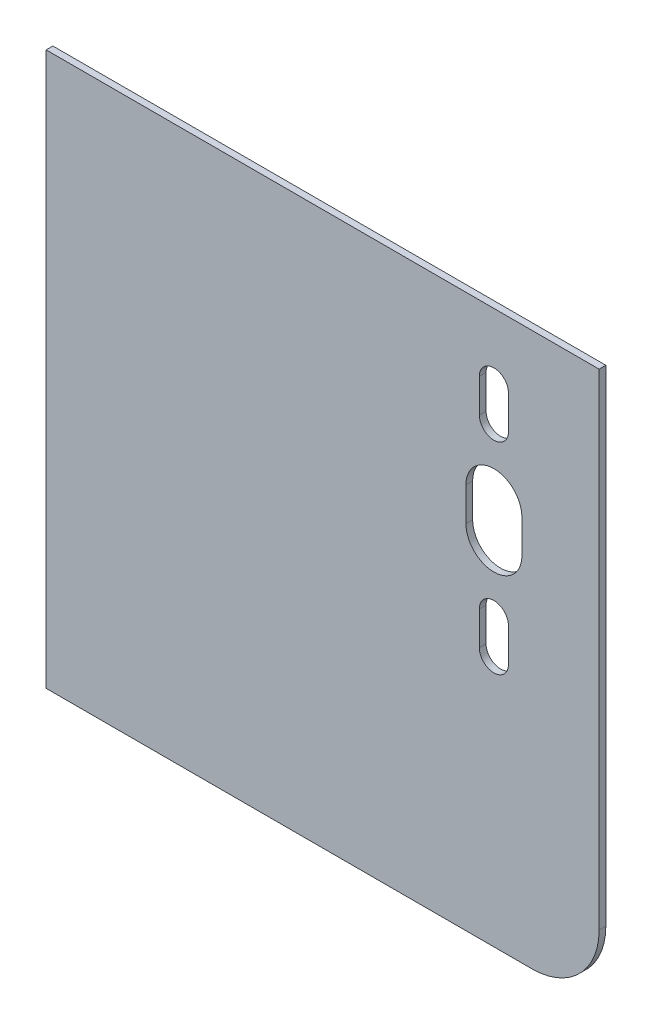
SolidWorks part; units mm, degrees
ref_plane "Plan de face" through (0, 0, 0) normal (0, 0, 1) x (1, 0, 0)
ref_plane "Plan de dessus" through (0, 0, 0) normal (0, 1, 0) x (1, 0, 0)
ref_plane "Plan de droite" through (0, 0, 0) normal (1, 0, 0) x (0, 0, -1)
sketch "Esquisse1" plane through (0, 0, 0) normal (0, 0, 1) x (1, 0, 0)
  line L0 (76.5, 110.5989) -> (76.5, -34.3036) construction
  line L1 (-123.5, -123.5) -> (123.5, -123.5)
  line L2 (-123.5, -123.5) -> (-123.5, 123.5)
  line L3 (-123.5, 123.5) -> (123.5, 123.5)
  line L4 (123.5, -123.5) -> (123.5, 123.5)
  line L5 (-123.5, -123.5) -> (123.5, 123.5) construction
  line L6 (-123.5, 123.5) -> (123.5, -123.5) construction
  circle A0 centre (76.5, 41.5) radius 12.5
  circle A1 centre (76.5, 86.5) radius 6.5
  circle A2 centre (76.5, -3.5) radius 6.5
  point P0 (0, 0)
  dimension "D3" = 25
  dimension "D4" = 13
  dimension "D5" = 13
  dimension "D6" = 90
  dimension "D7" = 45
  dimension "D8" = 200
  dimension "D9" = 82
  dimension "D1" = 247
  dimension "D2" = 247
extrude "Boss.-Extru.1" add sketch "Esquisse1" along normal blind 3
sketch "Esquisse2" plane through (0, 0, 3) normal (0, 0, 1) x (1, 0, 0)
  line L6 (-123.5, 123.5) -> (-123.5, -123.5) construction
  line L11 (-123.5, 38.5) -> (-120.5, 38.5)
  line L12 (-123.5, 38.5) -> (-123.5, -51.5)
  line L13 (-123.5, -51.5) -> (-120.5, -51.5)
  line L14 (-120.5, 38.5) -> (-120.5, -51.5)
  line L15 (123.5, 123.5) -> (-123.5, 123.5) construction
  line L17 (-123.5, 123.5) -> (-48.5, 123.5)
  line L18 (-123.5, 123.5) -> (-123.5, 120.5)
  line L19 (-123.5, 120.5) -> (-48.5, 120.5)
  line L20 (-48.5, 123.5) -> (-48.5, 120.5)
  line L21 (123.5, 123.5) -> (48.5, 123.5)
  line L22 (123.5, 123.5) -> (123.5, 120.5)
  line L23 (123.5, 120.5) -> (48.5, 120.5)
  line L24 (48.5, 123.5) -> (48.5, 120.5)
  dimension "D1" = 3
  dimension "D2" = 85
  dimension "D3" = 90
  dimension "D4" = 3
  dimension "D5" = 75
  dimension "D6" = 75
extrude "Enlèv. mat.-Extru.1" [suppressed] cut sketch "Esquisse2" against normal blind 3
fillet "Congé1" radius 30 1 edges at (123.5, -123.5, 1.5)
sketch "Esquisse3" plane through (0, 0, 3) normal (0, 0, 1) x (1, 0, 0)
  arc A0 (34.8239, 33.8757) -> (120.0673, 36.9665) centre (76.5, 61.5) ccw construction
  circle A1 centre (76.5, 41.5) radius 12.5 construction
  text T0 "Relevage" font "Century Gothic" height in points 48
  point P3 (114.0352, 28.468)
  point P5 (34.8239, 33.8757)
  point P6 (120.0673, 36.9665)
  dimension "D1" = 20
  dimension "D2" = 50
  dimension "D3" = 0
sketch "Esquisse4" plane through (0, 0, 0) normal (0, 0, -1) x (-1, 0, 0)
  line L0 (-76.5, 79) -> (-76.5, 94) construction
  line L1 (-83, 79) -> (-83, 94)
  line L2 (-70, 79) -> (-70, 94)
  line L3 (-76.5, -11) -> (-76.5, 4) construction
  line L4 (-83, -11) -> (-83, 4)
  line L5 (-70, -11) -> (-70, 4)
  line L6 (-76.5, 34) -> (-76.5, 49) construction
  line L7 (-89, 34) -> (-89, 49)
  line L8 (-64, 34) -> (-64, 49)
  arc A0 (-83, 79) -> (-70, 79) centre (-76.5, 79) ccw
  arc A1 (-70, 94) -> (-83, 94) centre (-76.5, 94) ccw
  arc A2 (-83, -11) -> (-70, -11) centre (-76.5, -11) ccw
  arc A3 (-70, 4) -> (-83, 4) centre (-76.5, 4) ccw
  arc A4 (-89, 34) -> (-64, 34) centre (-76.5, 34) ccw
  arc A5 (-64, 49) -> (-89, 49) centre (-76.5, 49) ccw
  point P2 (-76.5, 86.5)
  point P10 (-76.5, -3.5)
  point P18 (-76.5, 41.5)
  dimension "D1" = 6.5
  dimension "D3" = 6.5
  dimension "D5" = 12.5
  dimension "D2" = 15
  dimension "D4" = 15
  dimension "D6" = 15
extrude "Enlèv. mat.-Extru.2" cut sketch "Esquisse4" against normal blind 10
